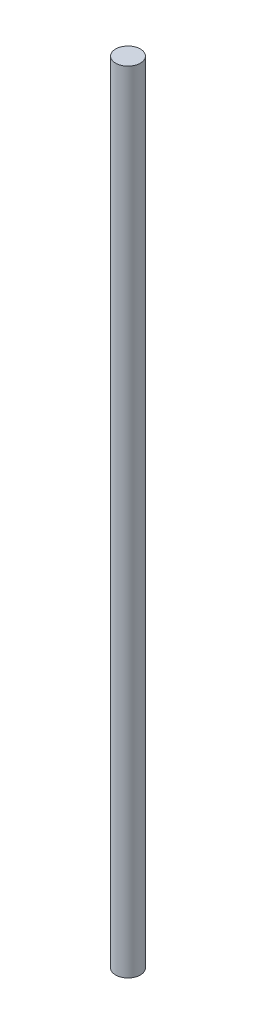
SolidWorks part; units mm, degrees
ref_plane "Front Plane" through (0, 0, 0) normal (0, 0, 1) x (1, 0, 0)
ref_plane "Top Plane" through (0, 0, 0) normal (0, 1, 0) x (1, 0, 0)
ref_plane "Right Plane" through (0, 0, 0) normal (1, 0, 0) x (0, 0, -1)
sketch "Sketch1" plane through (0, 0, 0) normal (0, 1, 0) x (1, 0, 0)
  circle A0 centre (0, 0) radius 4.7625
  dimension "D1" = 9.525
extrude "Boss-Extrude1" add sketch "Sketch1" along normal blind 304.8
